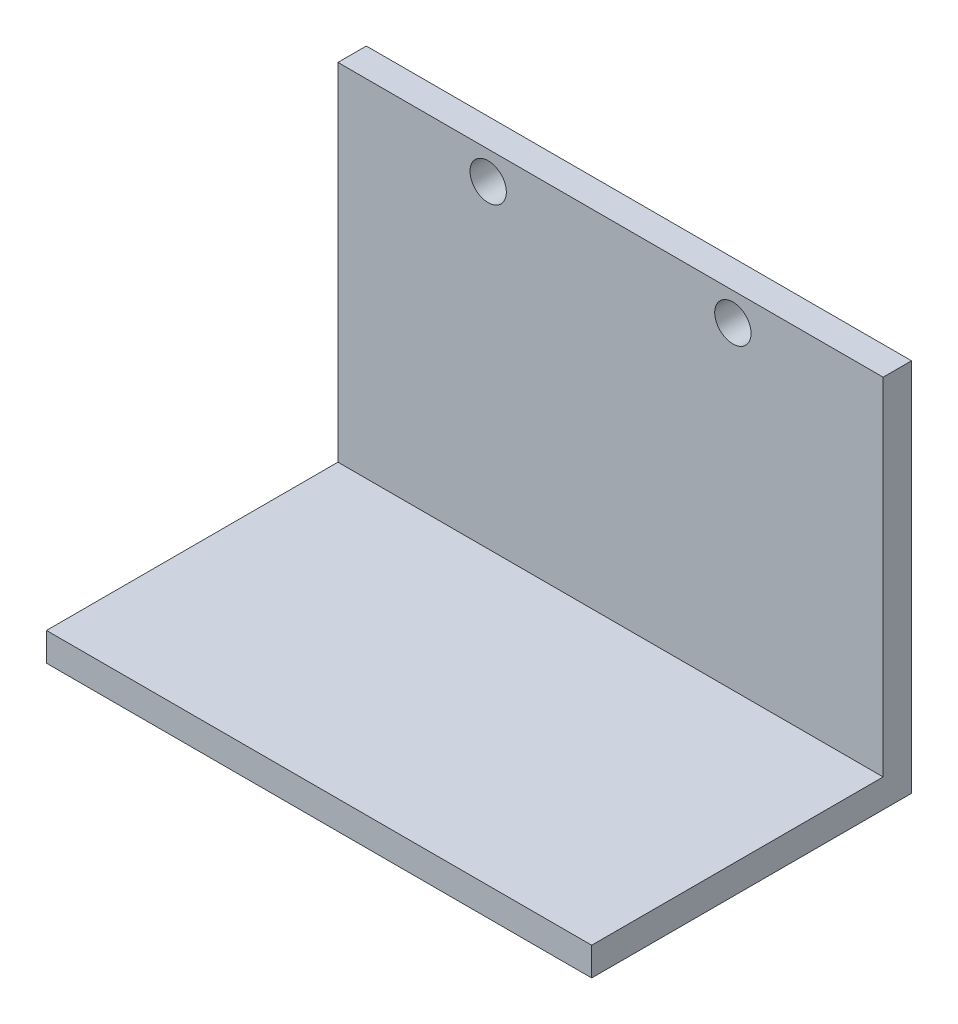
SolidWorks part; units mm, degrees
ref_plane "Front Plane" through (0, 0, 0) normal (0, 0, 1) x (1, 0, 0)
ref_plane "Top Plane" through (0, 0, 0) normal (0, 1, 0) x (1, 0, 0)
ref_plane "Right Plane" through (0, 0, 0) normal (1, 0, 0) x (0, 0, -1)
sketch "Sketch1" plane through (0, 0, 0) normal (1, 0, 0) x (0, 0, -1)
  line L0 (0, 0) -> (32.073, 0)
  line L1 (32.073, 0) -> (32.073, 38.1)
extrude "Extrude-Thin1" add sketch "Sketch1" along normal blind 60 thin
sketch "Esboço1" plane through (0, 0, -32.073) normal (0, 0, 1) x (1, 0, 0)
  circle A0 centre (16.5353, 35) radius 2
  circle A1 centre (43.4647, 35) radius 2
extrude "Corte-extrusão1" cut sketch "Esboço1" against normal blind 10
